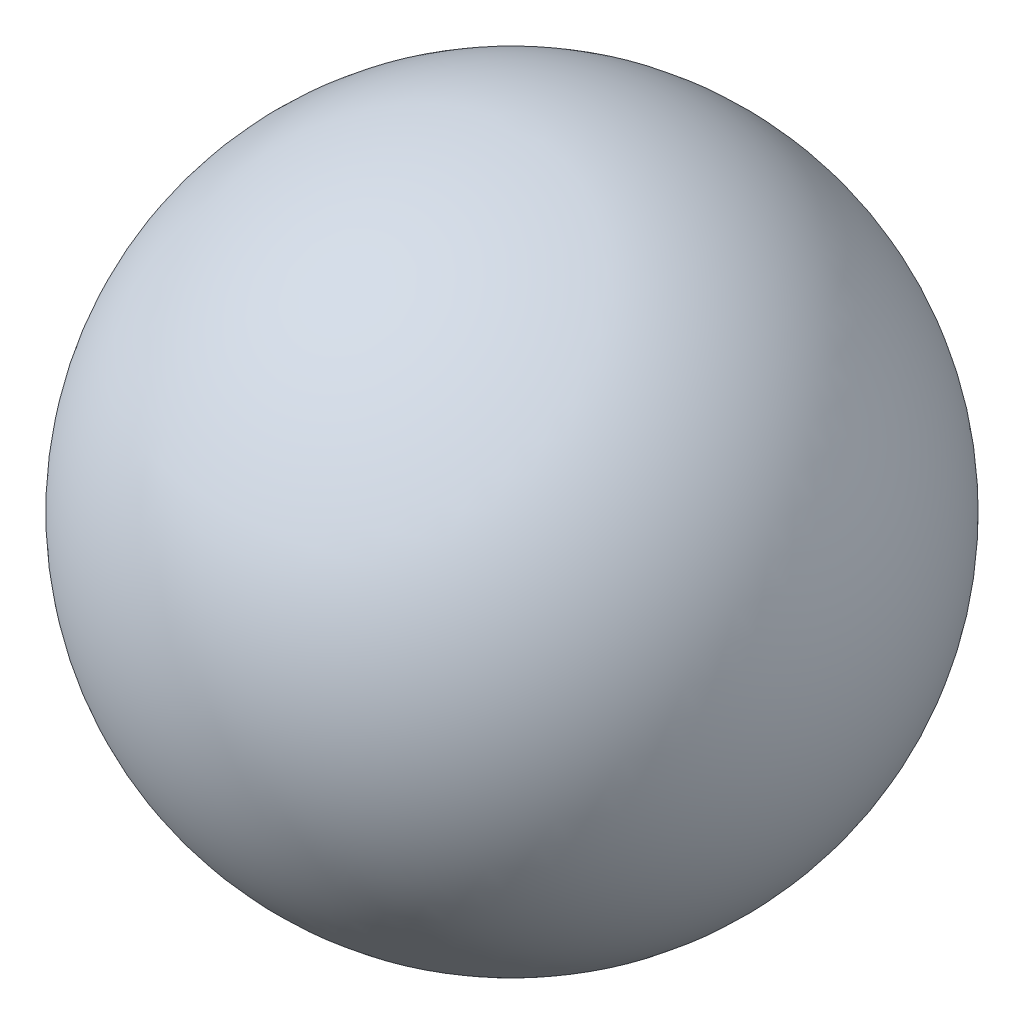
SolidWorks part; units mm, degrees
ref_plane "Front Plane" through (0, 0, 0) normal (0, 0, 1) x (1, 0, 0)
ref_plane "Top Plane" through (0, 0, 0) normal (0, 1, 0) x (1, 0, 0)
ref_plane "Right Plane" through (0, 0, 0) normal (1, 0, 0) x (0, 0, -1)
sketch "Sketch3" plane through (0, 0, 0) normal (0, 0, 1) x (1, 0, 0)
  line L0 (0, 0) -> (0, 19.05) construction
  line L1 (0, 0) -> (0, 19.05)
  arc A0 (0, 19.05) -> (0, 0) centre (0, 9.525) cw
  dimension "D1" = 9.525
revolve "Revolve1" add sketch "Sketch3" angle 360 about L0
